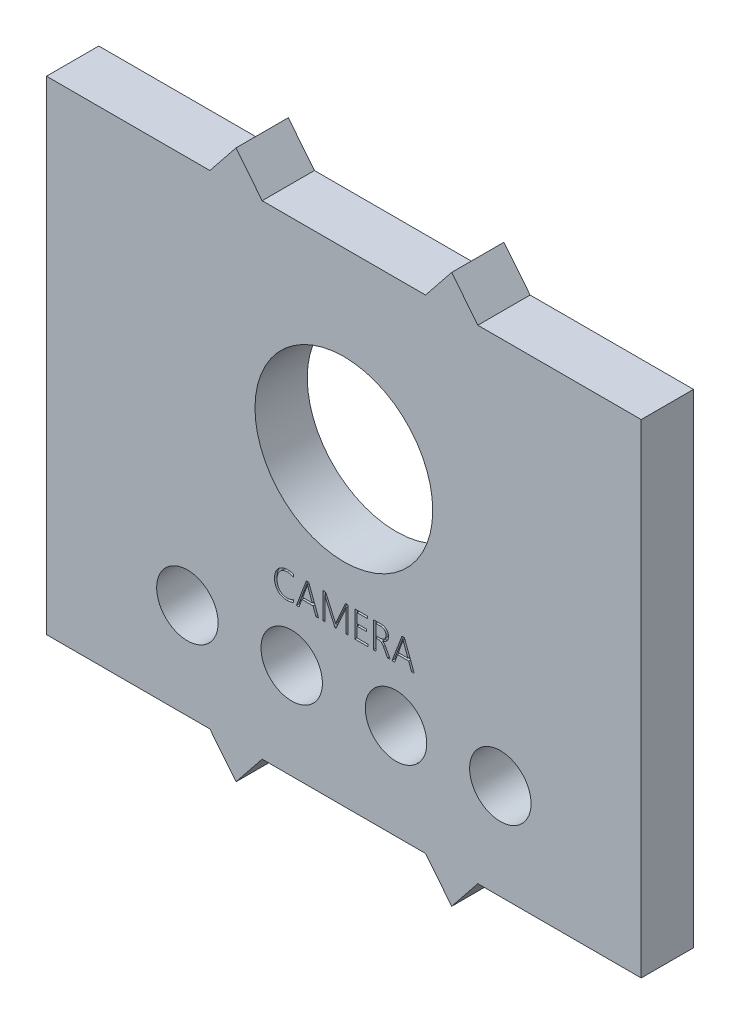
SolidWorks part; units mm, degrees
ref_plane "Front Plane" through (0, 0, 0) normal (0, 0, 1) x (1, 0, 0)
ref_plane "Top Plane" through (0, 0, 0) normal (0, 1, 0) x (1, 0, 0)
ref_plane "Right Plane" through (0, 0, 0) normal (1, 0, 0) x (0, 0, -1)
sketch "Sketch1" plane through (0, 0, 0) normal (0, 0, 1) x (1, 0, 0)
  line L0 (22.75, 37) -> (22.75, 14.7203) construction
  line L1 (0, 0) -> (45.5, 0)
  line L2 (0, 0) -> (0, 37)
  line L3 (0, 37) -> (45.5, 37)
  line L4 (45.5, 0) -> (45.5, 37)
  line L5 (12.5, 37) -> (14.5, 39.5)
  line L6 (14.5, 39.5) -> (16.5, 37)
  line L7 (31, 39.5) -> (29, 37)
  line L8 (33, 37) -> (31, 39.5)
  line L9 (0, 18.5) -> (57.9593, 18.5) construction
  line L10 (33, 0) -> (31, -2.5)
  line L11 (31, -2.5) -> (29, 0)
  line L12 (14.5, -2.5) -> (16.5, 0)
  line L13 (12.5, 0) -> (14.5, -2.5)
  point P9 (22.75, 37)
  point P16 (0, 18.5)
  point P17 (32, 38.25)
  point P18 (32, -1.25)
  dimension "D1" = 37
  dimension "D2" = 45.5
  dimension "D3" = 16.5
  dimension "D4" = 2.5
  dimension "D5" = 4
extrude "Basis" add sketch "Sketch1" along normal blind 4 contours L1 L4 L3 L2 | L6 L5 L3 | L3 L8 L7 | L1 L13 L12 | L11 L10 L1
sketch "Sketch2" plane through (0, 0, 4) normal (0, 0, 1) x (1, 0, 0)
  line L0 (16.5, 37) -> (29, 37) construction
  circle A0 centre (22.75, 23) radius 6.8
  point P5 (22.75, 37)
  dimension "D1" = 13.6
  dimension "D2" = 14
extrude "Camera gat " cut sketch "Sketch2" against normal up to surface (4 mm away) up to face at (22.75, 18.5, 0)
sketch "Sketch5" plane through (0, 0, 4) normal (0, 0, 1) x (1, 0, 0)
  line L0 (8.6574, 11.5) -> (36.8426, 11.5) construction
  line L1 (16.5, 37) -> (29, 37) construction
  line L2 (0, 0) -> (12.5, 0) construction
  text T0 "CAMERA" font "Yu Gothic UI Semilight" height 2
  point P2 (22.75, 11.5)
  point P5 (22.75, 37)
  dimension "D1" = 11.5
extrude "Cut-Extrude4" cut sketch "Sketch5" against normal blind 0.2
sketch "Sketch3" [suppressed] plane through (0, 0, 4) normal (0, 0, 1) x (1, 0, 0)
  line L0 (22.75, 37) -> (22.75, 0) construction
  line L1 (16.5, 37) -> (29, 37) construction
  line L2 (16.5, 0) -> (29, 0) construction
  line L3 (0, 37) -> (12.5, 37) construction
  circle A0 centre (9.8, 25.6) radius 7.95
  circle A1 centre (35.7, 25.6) radius 7.95
  dimension "D3" = 15.9
  dimension "D1" = 11.4
  dimension "D2" = 25.9
extrude "HR04 gat " [suppressed] cut sketch "Sketch3" against normal up to surface (4 mm away)
sketch "Sketch4" [suppressed] plane through (0, 0, 4) normal (0, 0, 1) x (1, 0, 0)
  line L0 (7.7992, 12.9938) -> (37.7008, 12.9938) construction
  line L1 (16.5, 37) -> (29, 37) construction
  text T0 "AFSTAND SENSOR" font "Yu Gothic UI Semilight" height 3.5
  point P5 (22.75, 12.9938)
  point P8 (22.75, 37)
extrude "Afstand sensor" [suppressed] cut sketch "Sketch4" against normal blind 0.2
sketch "Sketch6" [suppressed] plane through (0, 0, 4) normal (0, 0, 1) x (1, 0, 0)
  line L4 (16.5, 37) -> (29, 37) construction
  point P0 (22.75, 31.8)
  point P3 (22.75, 37)
  line B0 (9.1, 31.8) -> (36.4, 31.8)
  line B1 (9.1, 31.8) -> (9.1, 16.3191)
  line B2 (9.1, 16.3191) -> (36.4, 16.3191)
  line B3 (36.4, 31.8) -> (36.4, 16.3191)
  circle B4 centre (11.1, 34.0981) radius 1.5
  circle B5 centre (34.4, 34.0981) radius 1.5
  circle B6 centre (34.4, 10.2981) radius 1.5
  circle B7 centre (11.1, 10.2981) radius 1.5
  dimension "D1" = 5.2
sketch_block_instance "Block1-1" [suppressed]
sketch_block "Block1" parameters "D1"=3, "D2"=3, "D3"=3, "D4"=3
extrude "Cut-Extrude5" [suppressed] cut sketch "Sketch6" against normal up to surface (4 mm away)
sketch "Sketch7" [suppressed] plane through (0, 0, 4) normal (0, 0, 1) x (1, 0, 0)
  line L0 (-2.0092, 11.0348) -> (47.5092, 11.0348) construction
  line L1 (16.5, 37) -> (29, 37) construction
  text T0 "oled scherm " font "Yu Gothic UI Semilight" height 3.5
  point P4 (22.75, 37)
  point P5 (22.75, 11.0348)
extrude "Cut-Extrude6" [suppressed] cut sketch "Sketch7" against normal blind 0.2
sketch "Sketch9" [suppressed] plane through (0, 0, 4) normal (0, 0, 1) x (1, 0, 0)
  line L0 (15.4564, 12.6867) -> (24.4394, 12.6867) construction
  text T0 "V0.2"
extrude "Cut-Extrude8" [suppressed] cut sketch "Sketch9" against normal blind 0.2
sketch "Sketch10" plane through (0, 0, 4) normal (0, 0, 1) x (1, 0, 0)
  line L0 (0, 0) -> (0, 7.3308) construction
  line L1 (0, 0) -> (0, 37) construction
  line L2 (0, 7.3308) -> (10.78, 7.3308) construction
  line L3 (10.78, 7.3308) -> (18.76, 7.3308) construction
  line L4 (18.76, 7.3308) -> (26.74, 7.3308) construction
  line L5 (26.74, 7.3308) -> (34.72, 7.3308) construction
  line L6 (34.72, 7.3308) -> (45.5, 7.3308) construction
  line L7 (45.5, 0) -> (45.5, 37) construction
  circle A0 centre (10.78, 7.3308) radius 2.35
  circle A1 centre (18.76, 7.3308) radius 2.35
  circle A2 centre (26.74, 7.3308) radius 2.35
  circle A3 centre (34.72, 7.3308) radius 2.35
  dimension "D1" = 4.7
  dimension "D2" = 7.98
extrude "Cut-Extrude9" cut sketch "Sketch10" against normal blind 10
